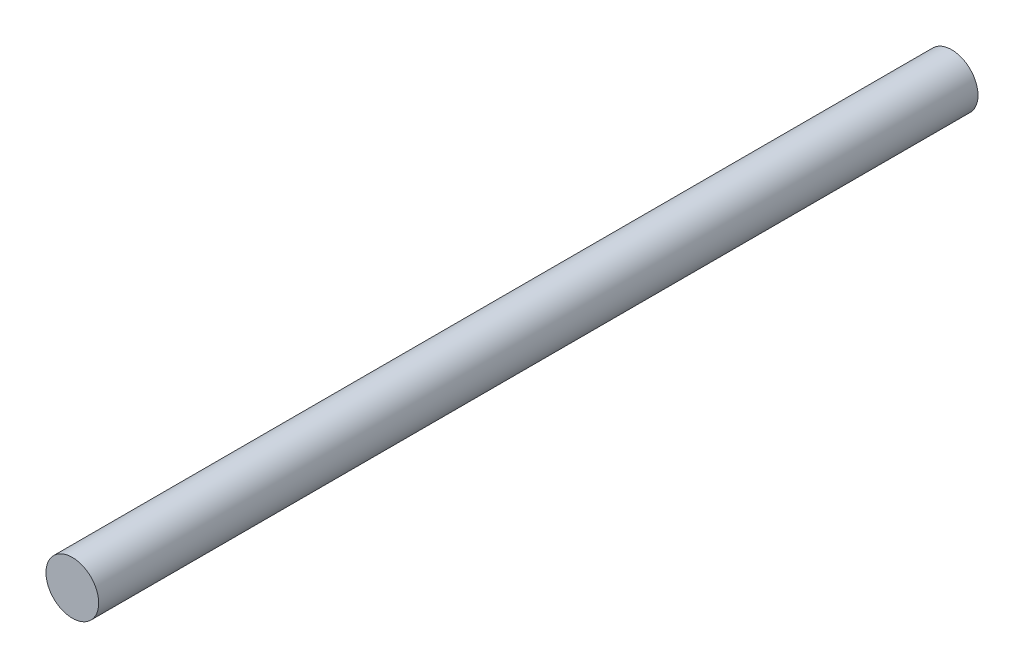
SolidWorks part; units mm, degrees
ref_plane "前视基准面" through (0, 0, 0) normal (0, 0, 1) x (1, 0, 0)
ref_plane "上视基准面" through (0, 0, 0) normal (0, 1, 0) x (1, 0, 0)
ref_plane "右视基准面" through (0, 0, 0) normal (1, 0, 0) x (0, 0, -1)
other "Configuration Table"
sketch "草图1" plane through (0, 0, 0) normal (0, 0, 1) x (1, 0, 0)
  circle A0 centre (0, 0) radius 1.5
  dimension "D1" = 3
extrude "凸台-拉伸1" add sketch "草图1" against normal blind 50
